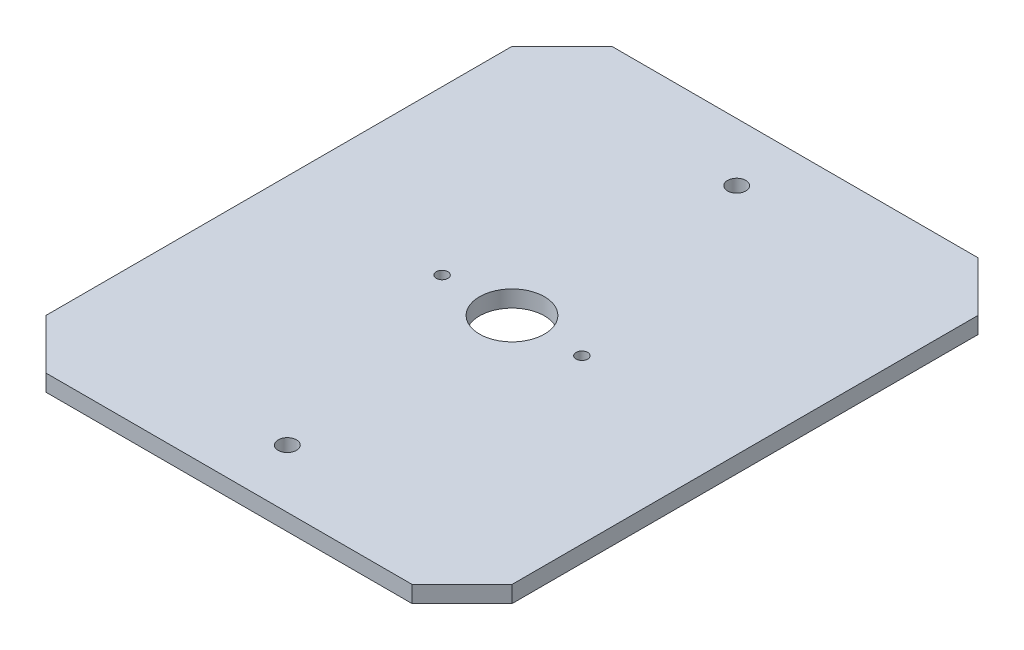
SolidWorks part; units mm, degrees
ref_plane "Front Plane" through (0, 0, 0) normal (0, 0, 1) x (1, 0, 0)
ref_plane "Top Plane" through (0, 0, 0) normal (0, 1, 0) x (1, 0, 0)
ref_plane "Right Plane" through (0, 0, 0) normal (1, 0, 0) x (0, 0, -1)
sketch "Sketch1" plane through (0, 0, 0) normal (0, 1, 0) x (1, 0, 0)
  line L1 (70, 85) -> (-70, 85)
  line L2 (70, 85) -> (70, -85)
  line L3 (70, -85) -> (-70, -85)
  line L4 (-70, 85) -> (-70, -85)
  line L5 (70, 85) -> (-70, -85) construction
  line L6 (70, -85) -> (-70, 85) construction
  point P0 (0, 0)
  dimension "D1" = 140
  dimension "D2" = 170
extrude "Boss-Extrude1" add sketch "Sketch1" along normal blind 5
chamfer "Chamfer1" distance 15 angle 45 4 edges at (70, 2.5, -85) (70, 2.5, 85) (-70, 2.5, 85) (-70, 2.5, -85)
sketch "Sketch2" plane through (0, 5, 0) normal (0, 1, 0) x (1, 0, 0)
  circle A0 centre (0, 0) radius 9.75
  dimension "D1" = 19.5
extrude "Cut-Extrude1" cut sketch "Sketch2" against normal blind 5
sketch "Sketch3" plane through (0, 5, 0) normal (0, 1, 0) x (1, 0, 0)
  line L0 (-55, -85) -> (55, -85) construction
  line L1 (-70, 0) -> (70, 0) construction
  line L2 (-70, 70) -> (-70, -70) construction
  line L3 (70, -70) -> (70, 70) construction
  circle A0 centre (0, -67.5) radius 2.75
  circle A1 centre (0, 67.5) radius 2.75
  dimension "D1" = 5.5
  dimension "D2" = 17.5
extrude "Cut-Extrude2" cut sketch "Sketch3" against normal blind 40
sketch "Sketch4" plane through (0, 5, 0) normal (0, 1, 0) x (1, 0, 0)
  line L0 (0, 0) -> (0, -42.7841) construction
  circle A0 centre (-21, 0) radius 1.75
  circle A1 centre (21, 0) radius 1.75
  dimension "D1" = 3.5
  dimension "D2" = 21
extrude "Cut-Extrude3" cut sketch "Sketch4" against normal through all
